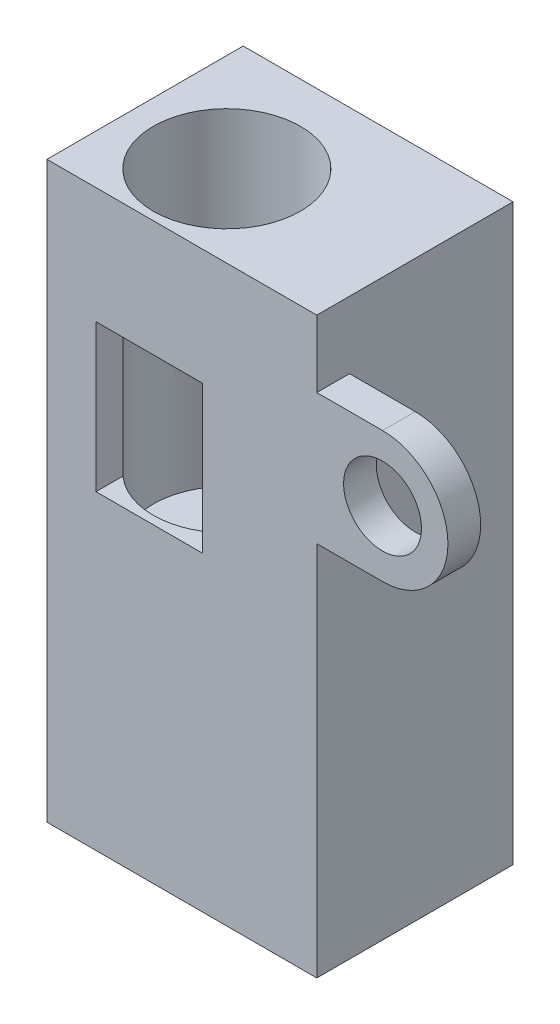
SolidWorks part; units mm, degrees
ref_plane "Front Plane" through (0, 0, 0) normal (0, 0, 1) x (1, 0, 0)
ref_plane "Top Plane" through (0, 0, 0) normal (0, 1, 0) x (1, 0, 0)
ref_plane "Right Plane" through (0, 0, 0) normal (1, 0, 0) x (0, 0, -1)
sketch "Sketch1" plane through (0, 0, 0) normal (1, 0, 0) x (0, 0, -1)
  line L0 (0, 0) -> (0, 37.1)
  line L1 (0, 37.1) -> (-10.6066, 47.7066)
  line L2 (0, 0) -> (12, 0)
  line L3 (12, 0) -> (12, 47.7066)
  line L4 (12, 47.7066) -> (-10.6066, 47.7066)
extrude "Boss-Extrude4" add sketch "Sketch1" along normal blind 16.5
sketch "Sketch4" plane through (0, 0, 0) normal (-1, 0, 0) x (0, 0, 1)
  line L0 (0, 37.1) -> (0, 47.7066)
  line L1 (-12, 47.7066) -> (10.6066, 47.7066) construction
  line L2 (0, 47.7066) -> (10.6066, 47.7066)
  line L3 (10.6066, 47.7066) -> (0, 37.1)
extrude "Cut-Extrude2" cut sketch "Sketch4" against normal blind 1.5
sketch "Sketch5" plane through (16.5, 0, 0) normal (1, 0, 0) x (0, 0, -1)
  line L0 (0, 37.1) -> (-3.567, 40.667)
  line L1 (-10.6066, 47.7066) -> (0, 37.1) construction
  line L2 (-3.567, 40.667) -> (-4.0973, 41.1973)
  line L3 (-4.0973, 41.1973) -> (-3.0366, 42.2579)
  line L4 (-3.0366, 42.2579) -> (-4.4508, 43.6722)
  line L5 (-4.4508, 43.6722) -> (-2.6831, 45.4399)
  line L6 (-3.567, 40.667) -> (-2.8598, 39.9598)
  line L7 (-2.8598, 39.9598) -> (-1.7992, 41.0205)
  line L12 (-2.6831, 45.4399) -> (0, 42.7569)
  line L13 (-1.7992, 41.0205) -> (0, 39.2213)
  line L14 (0, 39.2213) -> (0, 42.7569)
  line M14 (-10.6066, 47.7066) -> (0, 37.1)
extrude "Cut-Extrude4" cut sketch "Sketch5" against normal through all contours L13 L14 L12 L5 L4 L3 L7 M14
sketch "Sketch6" plane through (16.5, 0, 0) normal (1, 0, 0) x (0, 0, -1)
  line L0 (12, 0) -> (12, 2)
  line L1 (12, 0) -> (12, 47.7066) construction
  line L2 (12, 2) -> (0, 2)
  line L3 (0, 37.1) -> (0, 0) construction
  line L4 (0, 2) -> (0, 0)
  line L5 (0, 0) -> (12, 0)
extrude "Cut-Extrude5" cut sketch "Sketch6" against normal through all
sketch "Sketch9" plane through (0, 0, 0) normal (0, 0, 1) x (1, 0, 0)
  line L0 (16.5, 2) -> (16.5, 29)
  line L1 (16.5, 37.1) -> (16.5, 2) construction
  line L2 (16.5, 29) -> (20.5182, 29)
  line L3 (20.5182, 33) -> (16.5, 33)
  line L4 (16.5, 33) -> (16.5, 25)
  line L5 (16.5, 25) -> (20.5182, 25)
  arc A0 (20.5182, 33) -> (20.5182, 25) centre (20.5182, 29) cw
extrude "Boss-Extrude5" add sketch "Sketch9" against normal blind 2
sketch "Sketch10" plane through (0, 0, -2) normal (0, 0, -1) x (-1, 0, 0)
  line L0 (-20.5182, 33) -> (-20.5182, 29)
  circle A0 centre (-20.5182, 29) radius 2.3813
extrude "Cut-Extrude6" cut sketch "Sketch10" against normal through all
sketch "Sketch11" plane through (16.5, 0, 0) normal (1, 0, 0) x (0, 0, -1)
  line L0 (0, 37.1) -> (-10.6066, 47.7066)
  line L1 (-10.6066, 47.7066) -> (12, 47.7066)
  line L2 (0, 37.1) -> (12, 37.1)
  line L3 (12, 2) -> (12, 47.7066) construction
  line L4 (12, 37.1) -> (12, 47.7066)
extrude "Cut-Extrude7" cut sketch "Sketch11" against normal through all
sketch "Sketch12" plane through (0, 2, 0) normal (0, -1, 0) x (1, 0, 0)
  line L0 (16.5, 0) -> (16.5, -6)
  line L1 (16.5, -12) -> (16.5, 0) construction
  line L2 (16.5, -6) -> (8.25, -6)
  circle A0 centre (8.25, -6) radius 2.3813
extrude "Cut-Extrude8" cut sketch "Sketch12" against normal blind 6.35
sketch "Sketch13" plane through (0, 37.1, 0) normal (0, 1, 0) x (1, 0, 0)
  line L0 (0, 0) -> (6, 0)
  line L1 (16.5, 0) -> (0, 0) construction
  line L2 (6, 0) -> (6, 5)
  circle A1 centre (6, 5) radius 4.5
extrude "Cut-Extrude13" cut sketch "Sketch13" against normal blind 20
sketch "Sketch14" plane through (0, 0, 0) normal (0, 0, 1) x (1, 0, 0)
  line L0 (16.5, 2) -> (9.5, 2)
  line L1 (0, 2) -> (16.5, 2) construction
  line L2 (9.5, 2) -> (9.5, 21)
  line L3 (9.5, 21) -> (3, 21)
  line L4 (3, 21) -> (3, 30)
  line L5 (3, 30) -> (9.5, 30)
  line L6 (9.5, 30) -> (9.5, 21)
extrude "Cut-Extrude14" cut sketch "Sketch14" against normal blind 6 contours L6 L5 L4 L3
